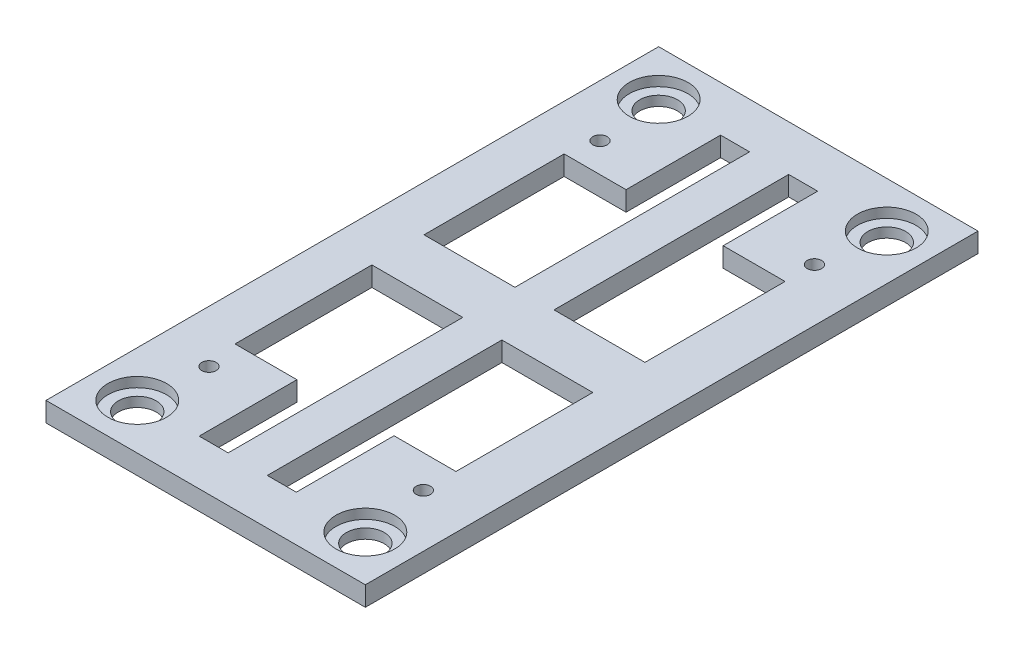
SolidWorks part; units mm, degrees
ref_plane "前视基准面" through (0, 0, 0) normal (0, 0, 1) x (1, 0, 0)
ref_plane "上视基准面" through (0, 0, 0) normal (0, 1, 0) x (1, 0, 0)
ref_plane "右视基准面" through (0, 0, 0) normal (1, 0, 0) x (0, 0, -1)
sketch "草图1" plane through (0, 0, 0) normal (0, 1, 0) x (1, 0, 0)
  line L0 (-35, 4) -> (-35, 25.5)
  line L1 (-1.1, 25.5) -> (-10.6, 25.5)
  line L2 (-10.6, 25.5) -> (-10.6, 40)
  line L3 (-21.05, 40) -> (-21.05, 4)
  line L4 (-1.1, 25.5) -> (-1.1, 4)
  line L5 (-1.1, -25) -> (-10.6, -25)
  line L6 (0, 40) -> (-1.1, 40)
  line L7 (-1.1, 40) -> (-1.1, 30) construction
  line L8 (-35, 40) -> (-34, 40)
  line L9 (-34, 40) -> (-34, 30) construction
  line L10 (-35, -40) -> (-34, -40)
  line L11 (-34, -40) -> (-34, -30) construction
  line L12 (0, -40) -> (-1.1, -40)
  line L13 (-1.1, -40) -> (-1.1, -30) construction
  line L14 (-10.6, -25) -> (-10.6, -40)
  line L15 (-21.05, 4) -> (-35, 4)
  line L16 (-1.1, -25) -> (-1.1, -4)
  line L17 (-42, 0) -> (-42, 47)
  line L18 (-42, 0) -> (-42, -47)
  line L19 (-42, -47) -> (0, -47)
  line L20 (0, -47) -> (7, -47)
  line L21 (0, 47) -> (-42, 47)
  line L22 (7, -47) -> (7, 47)
  line L23 (-35, -4) -> (-35, -25)
  line L24 (-25.5, -25) -> (-35, -25)
  line L25 (-25.5, -40) -> (-25.5, -25)
  line L26 (7, 47) -> (0, 47)
  line L29 (-15.05, 4) -> (-15.05, 40)
  line L30 (-25.5, 40) -> (-25.5, 25.5)
  line L32 (-25.5, 25.5) -> (-35, 25.5)
  line L33 (-21.05, 40) -> (-25.5, 40)
  line L34 (-15.05, 40) -> (-10.6, 40)
  line L35 (-15.05, 4) -> (-1.1, 4)
  line L36 (-21.05, -40) -> (-21.05, -4)
  line L37 (-21.05, -4) -> (-35, -4)
  line L38 (-25.5, -40) -> (-21.05, -40)
  line L39 (-15.05, -40) -> (-10.6, -40)
  line L40 (-15.05, -4) -> (-1.1, -4)
  line L41 (-15.05, -4) -> (-15.05, -40)
  circle A0 centre (-35, 40) radius 2.9
  circle A1 centre (0, 40) radius 2.9
  circle A2 centre (-35, -40) radius 2.9
  circle A3 centre (0, -40) radius 2.9
  circle A4 centre (-34, 30) radius 1.1
  circle A5 centre (-1.1, 30) radius 1.1
  circle A6 centre (-1.1, -30) radius 1.1
  circle A7 centre (-34, -30) radius 1.1
extrude "凸台-拉伸1" add sketch "草图1" along normal blind 3
sketch "草图2" plane through (0, 3, 0) normal (0, 1, 0) x (1, 0, 0)
  circle A0 centre (-35, 40) radius 4.5
  circle A1 centre (0, 40) radius 4.5
  circle A2 centre (0, -40) radius 4.5
  circle A3 centre (-35, -40) radius 4.5
extrude "切除-拉伸1" cut sketch "草图2" against normal blind 1.5
